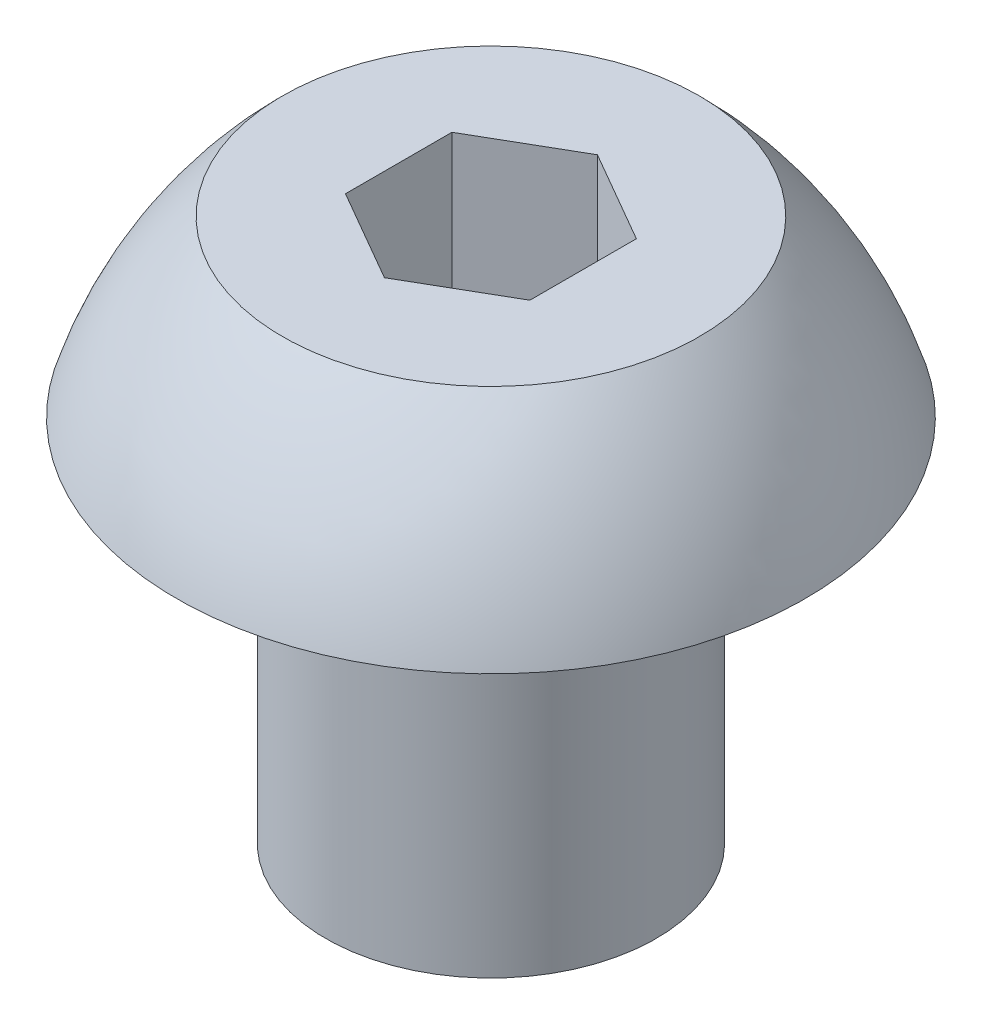
SolidWorks part; units mm, degrees
material "AISI Type 316L stainless steel"
ref_plane "Front Plane" through (0, 0, 0) normal (0, 0, 1) x (1, 0, 0)
ref_plane "Top Plane" through (0, 0, 0) normal (0, 1, 0) x (1, 0, 0)
ref_plane "Right Plane" through (0, 0, 0) normal (1, 0, 0) x (0, 0, -1)
sketch "Sketch1" plane through (0, 0, 0) normal (0, 0, 1) x (1, 0, 0)
  line L0 (-1.4224, 0) -> (-2.7051, 0)
  line L1 (-1.4224, 0) -> (-1.4224, -3.175)
  line L2 (0, -3.175) -> (0, 1.4986)
  line L3 (0, 1.4986) -> (-1.7948, 1.4986)
  line L4 (-1.4224, -3.175) -> (0, -3.175)
  arc A0 (-2.7051, 0) -> (-1.7948, 1.4986) centre (0.7001, -1.0427) cw
  dimension "D1" = 3.175
  dimension "D2" = 1.4986
  dimension "D3" = 2.7051
  dimension "D4" = 1.4224
  dimension "D5" = 1.7948
revolve "Revolve1" add sketch "Sketch1" angle 360 about L2
sketch "Sketch2" plane through (0, 1.4986, 0) normal (0, 1, 0) x (1, 0, 0)
  line L0 (0, 0) -> (0, 0.9165) construction
  line L1 (-0.7938, 0.4583) -> (-0.7937, -0.4583)
  line L2 (-0.7937, -0.4583) -> (0, -0.9165)
  line L3 (0, -0.9165) -> (0.7937, -0.4583)
  line L4 (0.7937, -0.4583) -> (0.7937, 0.4583)
  line L5 (0.7937, 0.4583) -> (0, 0.9165)
  line L6 (0, 0.9165) -> (-0.7938, 0.4583)
  circle A0 centre (0, 0) radius 0.7937 construction
  dimension "D1" = 1.5875
extrude "Cut-Extrude1" cut sketch "Sketch2" against normal blind 1.27
